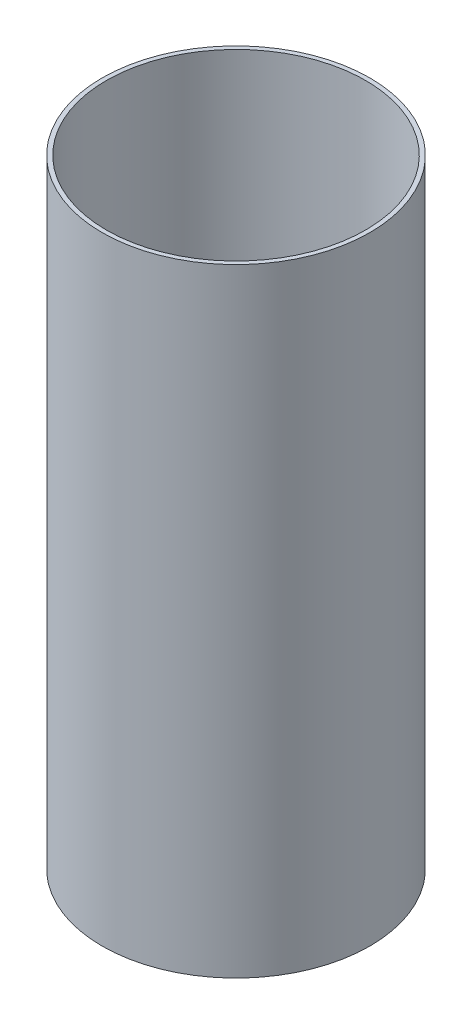
SolidWorks part; units mm, degrees
ref_plane "Front Plane" through (0, 0, 0) normal (0, 0, 1) x (1, 0, 0)
ref_plane "Top Plane" through (0, 0, 0) normal (0, 1, 0) x (1, 0, 0)
ref_plane "Right Plane" through (0, 0, 0) normal (1, 0, 0) x (0, 0, -1)
sketch "Sketch1" plane through (0, 0, 0) normal (0, 1, 0) x (1, 0, 0)
  circle A0 centre (0, 0) radius 49.55
  circle A1 centre (0, 0) radius 47.95
  dimension "D1" = 99.1
  dimension "D2" = 95.9
extrude "Boss-Extrude1" add sketch "Sketch1" along normal blind 228.6
